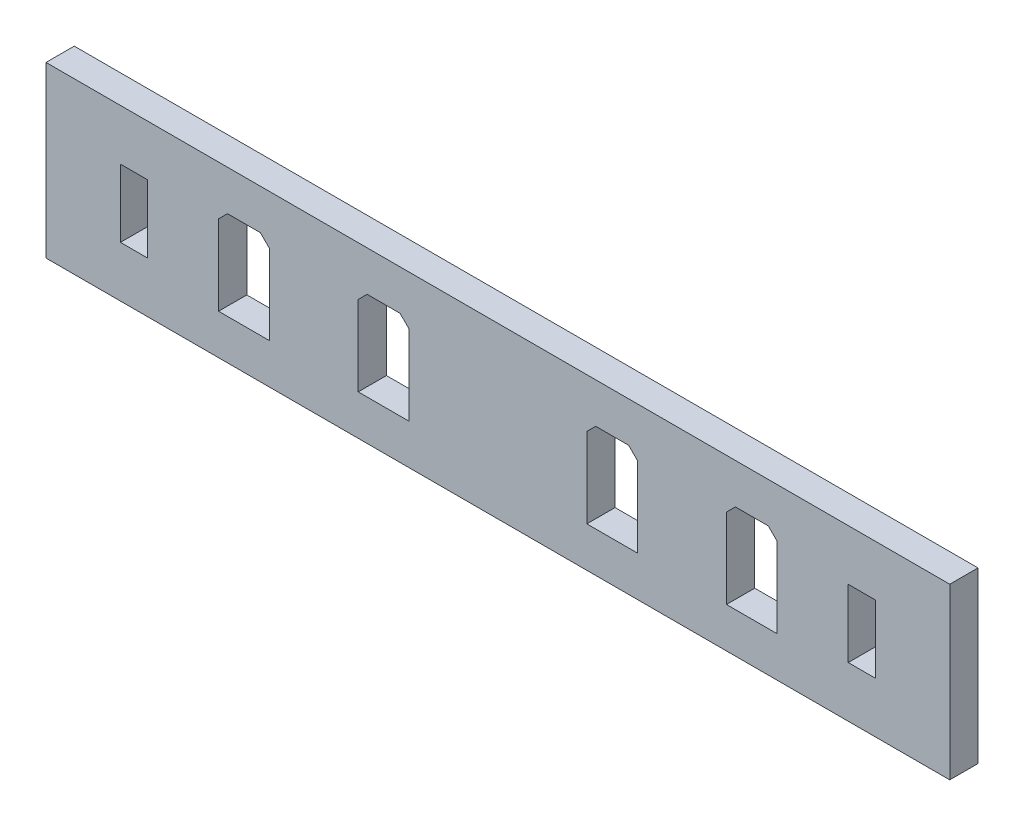
SolidWorks part; units mm, degrees
ref_plane "Front Plane" through (0, 0, 0) normal (0, 0, 1) x (1, 0, 0)
ref_plane "Top Plane" through (0, 0, 0) normal (0, 1, 0) x (1, 0, 0)
ref_plane "Right Plane" through (0, 0, 0) normal (1, 0, 0) x (0, 0, -1)
sketch "Sketch1" plane through (0, 0, 0) normal (0, 0, 1) x (1, 0, 0)
  line L1 (0, 0) -> (101.6, 0)
  line L2 (0, 0) -> (0, 19.05)
  line L3 (0, 19.05) -> (101.6, 19.05)
  line L4 (101.6, 0) -> (101.6, 19.05)
  dimension "D1" = 19.05
  dimension "D2" = 101.6
extrude "Boss-Extrude1" add sketch "Sketch1" along normal blind 3.175
sketch "Sketch2" plane through (0, 0, 3.175) normal (0, 0, 1) x (1, 0, 0)
  line L0 (0, 19.05) -> (0, 0) construction
  line L1 (8.3681, 13.335) -> (11.4161, 13.335)
  line L2 (8.3681, 13.335) -> (8.3681, 5.715)
  line L3 (8.3681, 5.715) -> (11.4161, 5.715)
  line L4 (11.4161, 13.335) -> (11.4161, 5.715)
  line L5 (50.8, 19.05) -> (50.8, 0) construction
  line L6 (101.6, 19.05) -> (0, 19.05) construction
  line L7 (0, 0) -> (101.6, 0) construction
  line L8 (93.2319, 5.715) -> (90.1839, 5.715)
  line L9 (90.1839, 13.335) -> (90.1839, 5.715)
  line L10 (93.2319, 13.335) -> (93.2319, 5.715)
  line L11 (93.2319, 13.335) -> (90.1839, 13.335)
  point P6 (9.8921, 5.715)
  point P7 (0, 9.525)
  point P8 (8.3681, 9.525)
  dimension "D1" = 8.3681
  dimension "D2" = 3.048
  dimension "D3" = 7.62
extrude "Cut-Extrude1" cut sketch "Sketch2" against normal through all
sketch "Sketch3" plane through (0, 0, 3.175) normal (0, 0, 1) x (1, 0, 0)
  line L0 (0, 19.05) -> (0, 0) construction
  line L1 (35.1, 14.525) -> (40.8, 14.525)
  line L2 (35.1, 14.525) -> (35.1, 4.525)
  line L3 (35.1, 4.525) -> (40.8, 4.525)
  line L4 (40.8, 14.525) -> (40.8, 4.525)
  line L5 (50.8, 19.05) -> (50.8, 0) construction
  line L6 (101.6, 19.05) -> (0, 19.05) construction
  line L7 (0, 0) -> (101.6, 0) construction
  line L8 (60.8, 14.525) -> (60.8, 4.525)
  line L9 (66.5, 4.525) -> (60.8, 4.525)
  line L10 (66.5, 14.525) -> (66.5, 4.525)
  line L11 (66.5, 14.525) -> (60.8, 14.525)
  line L12 (76.5, 14.525) -> (76.5, 4.525)
  line L13 (19.4, 14.525) -> (25.1, 14.525)
  line L14 (19.4, 14.525) -> (19.4, 4.525)
  line L15 (19.4, 4.525) -> (25.1, 4.525)
  line L16 (25.1, 14.525) -> (25.1, 4.525)
  line L17 (82.2, 4.525) -> (76.5, 4.525)
  line L18 (82.2, 14.525) -> (82.2, 4.525)
  line L19 (82.2, 14.525) -> (76.5, 14.525)
  point P4 (37.95, 4.525)
  point P7 (0, 9.525)
  point P8 (35.1, 9.525)
  point P23 (19.4, 9.525)
  dimension "D1" = 5.7
  dimension "D2" = 10
  dimension "D3" = 10
  dimension "D4" = 5.7
  dimension "D5" = 10
  dimension "D6" = 10
extrude "Cut-Extrude2" cut sketch "Sketch3" against normal through all
chamfer "Chamfer1" distance 1 angle 45 8 edges at (82.2, 14.525, 1.5875) (76.5, 14.525, 1.5875) (66.5, 14.525, 1.5875) (60.8, 14.525, 1.5875) (35.1, 14.525, 1.5875) (40.8, 14.525, 1.5875) (25.1, 14.525, 1.5875) (19.4, 14.525, 1.5875)
